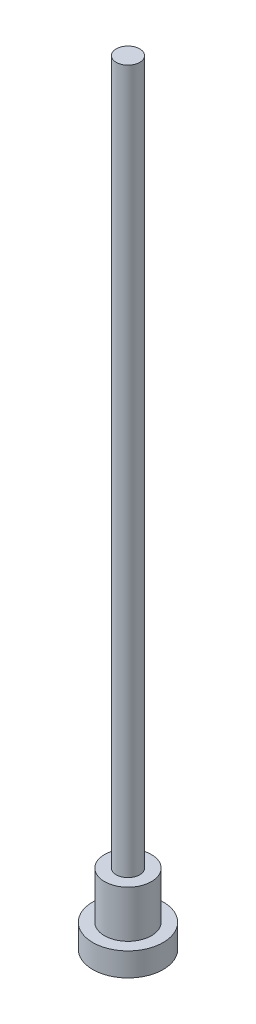
SolidWorks part; units mm, degrees
ref_plane "Front Plane" through (0, 0, 0) normal (0, 0, 1) x (1, 0, 0)
ref_plane "Top Plane" through (0, 0, 0) normal (0, 1, 0) x (1, 0, 0)
ref_plane "Right Plane" through (0, 0, 0) normal (1, 0, 0) x (0, 0, -1)
sketch "Sketch1" plane through (0, 0, 0) normal (0, 1, 0) x (1, 0, 0)
  circle A0 centre (0, 0) radius 1.5
  dimension "D1" = 3
extrude "Boss-Extrude1" add sketch "Sketch1" along normal blind 1
sketch "Sketch2" plane through (0, 1, 0) normal (0, 1, 0) x (1, 0, 0)
  circle A0 centre (0, 0) radius 1
  dimension "D1" = 2
extrude "Boss-Extrude3" add sketch "Sketch2" along normal blind 2
sketch "Sketch3" plane through (0, 3, 0) normal (0, 1, 0) x (1, 0, 0)
  circle A0 centre (0, 0) radius 0.5
  dimension "D1" = 1
extrude "Boss-Extrude4" add sketch "Sketch3" along normal blind 30
